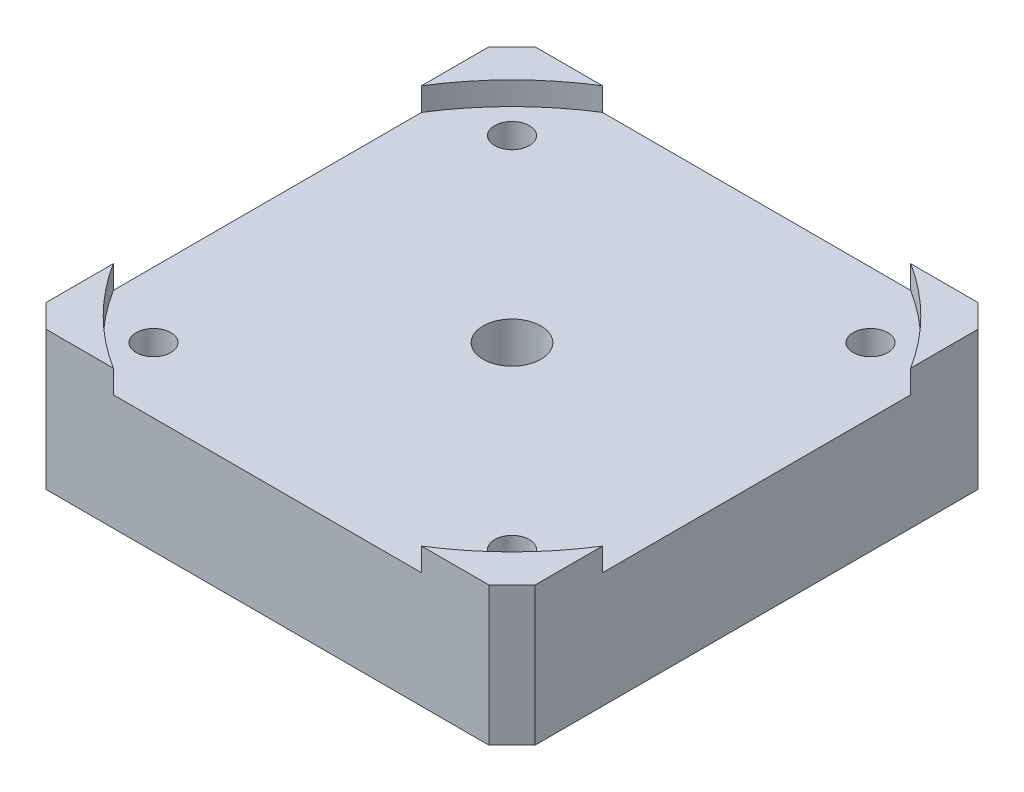
SolidWorks part; units mm, degrees
ref_plane "Alzado" through (0, 0, 0) normal (0, 0, 1) x (1, 0, 0)
ref_plane "Planta" through (0, 0, 0) normal (0, 1, 0) x (1, 0, 0)
ref_plane "Vista lateral" through (0, 0, 0) normal (1, 0, 0) x (0, 0, -1)
sketch "Croquis1" plane through (0, 0, 0) normal (0, 1, 0) x (1, 0, 0)
  line L1 (-21.15, -21.15) -> (21.15, -21.15)
  line L2 (-21.15, -21.15) -> (-21.15, 21.15)
  line L3 (-21.15, 21.15) -> (21.15, 21.15)
  line L4 (21.15, -21.15) -> (21.15, 21.15)
  line L5 (-21.15, -21.15) -> (21.15, 21.15) construction
  line L6 (-21.15, 21.15) -> (21.15, -21.15) construction
  point P0 (0, 0)
  dimension "D1" = 42.3
  dimension "D2" = 42.3
extrude "Saliente-Extruir1" add sketch "Croquis1" along normal blind 12
sketch "Croquis2" plane through (0, 12, 0) normal (0, 1, 0) x (1, 0, 0)
  line L0 (-21.15, 13.3296) -> (-21.15, -13.3296)
  line L2 (-13.3296, -21.15) -> (13.3296, -21.15)
  line L3 (-13.3296, 21.15) -> (13.3296, 21.15)
  line L4 (21.15, 13.3296) -> (21.15, -13.3296)
  line L5 (21.15, 21.15) -> (-21.15, 21.15) construction
  line L6 (-21.15, 21.15) -> (-21.15, -21.15) construction
  line L7 (-21.15, -21.15) -> (21.15, -21.15) construction
  line L9 (21.15, -21.15) -> (21.15, 21.15) construction
  arc A0 (-21.15, -13.3296) -> (-13.3296, -21.15) centre (0, 0) ccw
  arc A1 (-13.3296, 21.15) -> (-21.15, 13.3296) centre (0, 0) ccw
  arc A2 (21.15, 13.3296) -> (13.3296, 21.15) centre (0, 0) ccw
  arc A3 (13.3296, -21.15) -> (21.15, -13.3296) centre (0, 0) ccw
  dimension "D1" = 50
extrude "Cortar-Extruir1" cut sketch "Croquis2" against normal blind 2
chamfer "Chaflán1" distance 2 angle 45 4 edges at (21.15, 6, -21.15) (-21.15, 6, -21.15) (-21.15, 6, 21.15) (21.15, 6, 21.15)
sketch "Croquis3" plane through (0, 0, 0) normal (0, -1, 0) x (1, 0, 0)
  line L0 (-16.8431, 0) -> (13.1171, 0) construction
  line L1 (0, 0) -> (0, 17.375) construction
  circle A0 centre (-15.5, 15.5) radius 1.5
  circle A1 centre (-15.5, -15.5) radius 1.5
  circle A4 centre (15.5, -15.5) radius 1.5
  circle A5 centre (15.5, 15.5) radius 1.5
  dimension "D1" = 3
  dimension "D2" = 31
  dimension "D3" = 31
extrude "Cortar-Extruir2" cut sketch "Croquis3" against normal blind 10
sketch "Croquis4" plane through (0, 0, 0) normal (0, -1, 0) x (1, 0, 0)
  circle A0 centre (0, 0) radius 12
  dimension "D1" = 24
extrude "Cortar-Extruir3" cut sketch "Croquis4" against normal blind 2
sketch "Croquis5" plane through (0, 2, 0) normal (0, -1, 0) x (1, 0, 0)
  circle A0 centre (0, 0) radius 11
  dimension "D1" = 22
extrude "Saliente-Extruir2" add sketch "Croquis5" along normal blind 4
sketch "Croquis6" plane through (0, -2, 0) normal (0, -1, 0) x (1, 0, 0)
  circle A0 centre (0, 0) radius 3.5
  dimension "D1" = 7
extrude "Cortar-Extruir5" cut sketch "Croquis6" against normal blind 2 contours A0
sketch "Croquis7" plane through (0, 0, 0) normal (0, -1, 0) x (1, 0, 0)
  circle A0 centre (0, 0) radius 2.5
  dimension "D1" = 5
extrude "Cortar-Extruir6" cut sketch "Croquis7" against normal through all contours A0
thread "Rosca1" pitch 0.5 start angle 0, offset 0, length 4.5, pitch 0.5, diameter 3
ref_plane "Plano3" through (-14, 0, -15.5) normal (0, 0, 1) x (1, 0, 0)
sketch "Perfil de rosca3" plane through (-14, 0, -15.5) normal (0, 0, 1) x (1, 0, 0)
  line L0 (0, 0) -> (0, 0.5) construction
  line L1 (0, 0) -> (0.2706, 0.1562)
  line L2 (0.2706, 0.1562) -> (0.2706, 0.2187)
  line L3 (0.2706, 0.2187) -> (0, 0.375)
  line L4 (0.2706, 0.1875) -> (0, 0.1875) construction
  line L11 (0, 0) -> (0, 0.375)
  point P2 (0, 0)
  dimension "Pitch" = 0.5
  dimension "Profile_Angle" = 60
  dimension "Profile_Land" = 0.0625
  dimension "Profile_Height" = 0.2706
thread "Rosca2" pitch 0.5 start angle 0, offset 0, length 4.5, pitch 0.5, diameter 3
ref_plane "Plano4" through (-14, 0, 15.5) normal (0, 0, 1) x (1, 0, 0)
sketch "Perfil de rosca4" plane through (-14, 0, 15.5) normal (0, 0, 1) x (1, 0, 0)
  line L0 (0, 0) -> (0, 0.5) construction
  line L1 (0, 0) -> (0.2706, 0.1562)
  line L2 (0.2706, 0.1562) -> (0.2706, 0.2187)
  line L3 (0.2706, 0.2187) -> (0, 0.375)
  line L4 (0.2706, 0.1875) -> (0, 0.1875) construction
  line L11 (0, 0) -> (0, 0.375)
  point P2 (0, 0)
  dimension "Pitch" = 0.5
  dimension "Profile_Angle" = 60
  dimension "Profile_Land" = 0.0625
  dimension "Profile_Height" = 0.2706
thread "Rosca3" pitch 0.5 start angle 0, offset 0, length 4.5, pitch 0.5, diameter 3
ref_plane "Plano5" through (17, 0, 15.5) normal (0, 0, 1) x (1, 0, 0)
sketch "Perfil de rosca5" plane through (17, 0, 15.5) normal (0, 0, 1) x (1, 0, 0)
  line L0 (0, 0) -> (0, 0.5) construction
  line L1 (0, 0) -> (0.2706, 0.1562)
  line L2 (0.2706, 0.1562) -> (0.2706, 0.2187)
  line L3 (0.2706, 0.2187) -> (0, 0.375)
  line L4 (0.2706, 0.1875) -> (0, 0.1875) construction
  line L11 (0, 0) -> (0, 0.375)
  point P2 (0, 0)
  dimension "Pitch" = 0.5
  dimension "Profile_Angle" = 60
  dimension "Profile_Land" = 0.0625
  dimension "Profile_Height" = 0.2706
thread "Rosca4" pitch 0.5 start angle 0, offset 0, length 4.5, pitch 0.5, diameter 3
ref_plane "Plano6" through (17, 0, -15.5) normal (0, 0, 1) x (1, 0, 0)
sketch "Perfil de rosca6" plane through (17, 0, -15.5) normal (0, 0, 1) x (1, 0, 0)
  line L0 (0, 0) -> (0, 0.5) construction
  line L1 (0, 0) -> (0.2706, 0.1562)
  line L2 (0.2706, 0.1562) -> (0.2706, 0.2187)
  line L3 (0.2706, 0.2187) -> (0, 0.375)
  line L4 (0.2706, 0.1875) -> (0, 0.1875) construction
  line L11 (0, 0) -> (0, 0.375)
  point P2 (0, 0)
  dimension "Pitch" = 0.5
  dimension "Profile_Angle" = 60
  dimension "Profile_Land" = 0.0625
  dimension "Profile_Height" = 0.2706
